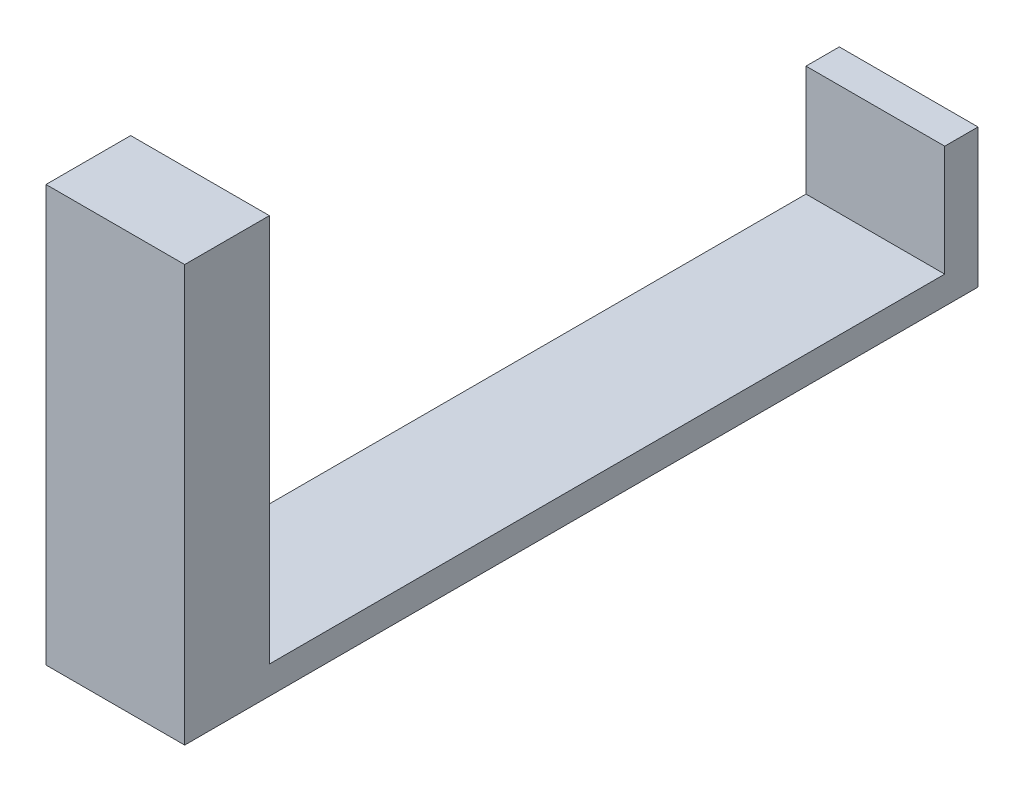
SolidWorks part; units mm, degrees
ref_plane "Front Plane" through (0, 0, 0) normal (0, 0, 1) x (1, 0, 0)
ref_plane "Top Plane" through (0, 0, 0) normal (0, 1, 0) x (1, 0, 0)
ref_plane "Right Plane" through (0, 0, 0) normal (1, 0, 0) x (0, 0, -1)
sketch "Sketch1" plane through (0, 0, 0) normal (0, 0, 1) x (1, 0, 0)
  line L0 (0, 0) -> (-250, 0)
  line L1 (-250, 0) -> (-250, 250)
  line L2 (-250, 250) -> (0, 250)
  line L3 (0, 250) -> (0, 0)
  dimension "D1" = 250
  dimension "D2" = 250
extrude "Boss-Extrude1" add sketch "Sketch1" along normal blind 60 contours L2 L3 L0 L1
sketch "Sketch2" plane through (0, 0, 60) normal (0, 0, 1) x (1, 0, 0)
  line L0 (0, 50.2337) -> (-250, 50.2337)
  line L1 (0, 250) -> (0, 0) construction
  line L2 (-250, 0) -> (-250, 250) construction
  line L3 (-250, 50.2337) -> (-250, 0)
  line L4 (-250, 0) -> (0, 0)
  line L5 (0, 0) -> (0, 50.2337)
extrude "Boss-Extrude2" add sketch "Sketch2" along normal blind 1370
sketch "Sketch3" plane through (0, 50.2337, 0) normal (0, 1, 0) x (1, 0, 0)
  line L0 (0, -1277.336) -> (-250, -1277.336)
  line L1 (0, -1430) -> (0, -60) construction
  line L2 (-250, -1430) -> (-250, -60) construction
  line L3 (-250, -1277.336) -> (-250, -1430)
  line L4 (-250, -1430) -> (0, -1430)
  line L5 (0, -1430) -> (0, -1277.336)
extrude "Boss-Extrude3" add sketch "Sketch3" along normal blind 700
